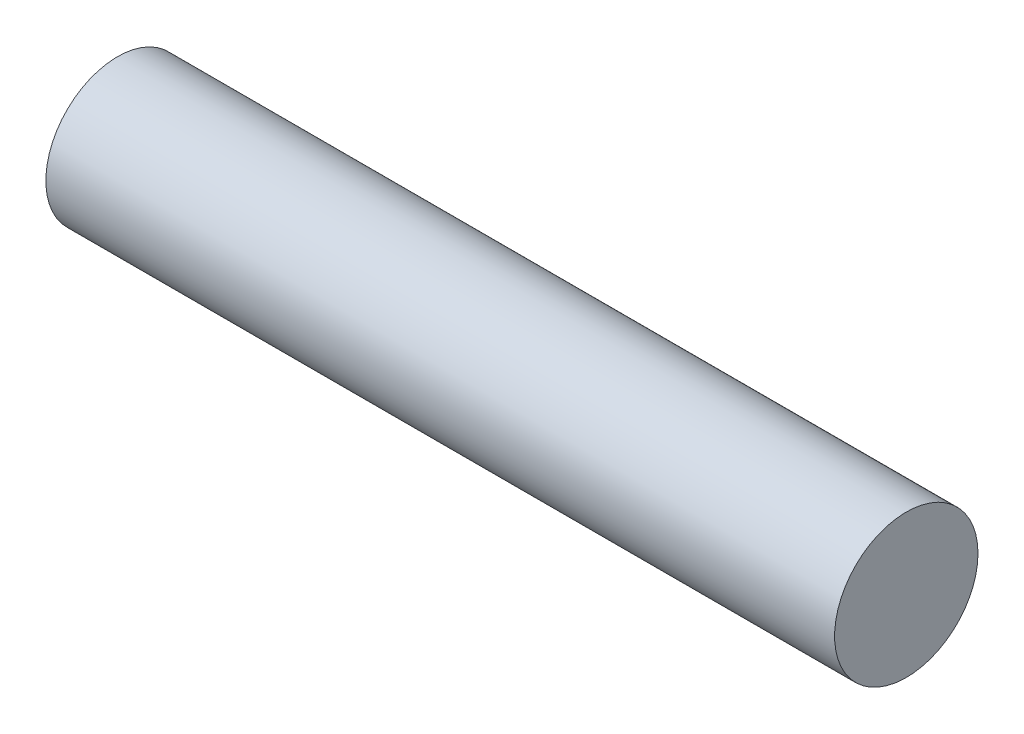
SolidWorks part; units mm, degrees
ref_plane "前视基准面" through (0, 0, 0) normal (0, 0, 1) x (1, 0, 0)
ref_plane "上视基准面" through (0, 0, 0) normal (0, 1, 0) x (1, 0, 0)
ref_plane "右视基准面" through (0, 0, 0) normal (1, 0, 0) x (0, 0, -1)
sketch "草图1" plane through (0, 0, 0) normal (1, 0, 0) x (0, 0, -1)
  circle A0 centre (0, 0) radius 1.5
  dimension "D1" = 3
extrude "凸台-拉伸1" add sketch "草图1" along normal blind 16.5
ref_point "点1"
